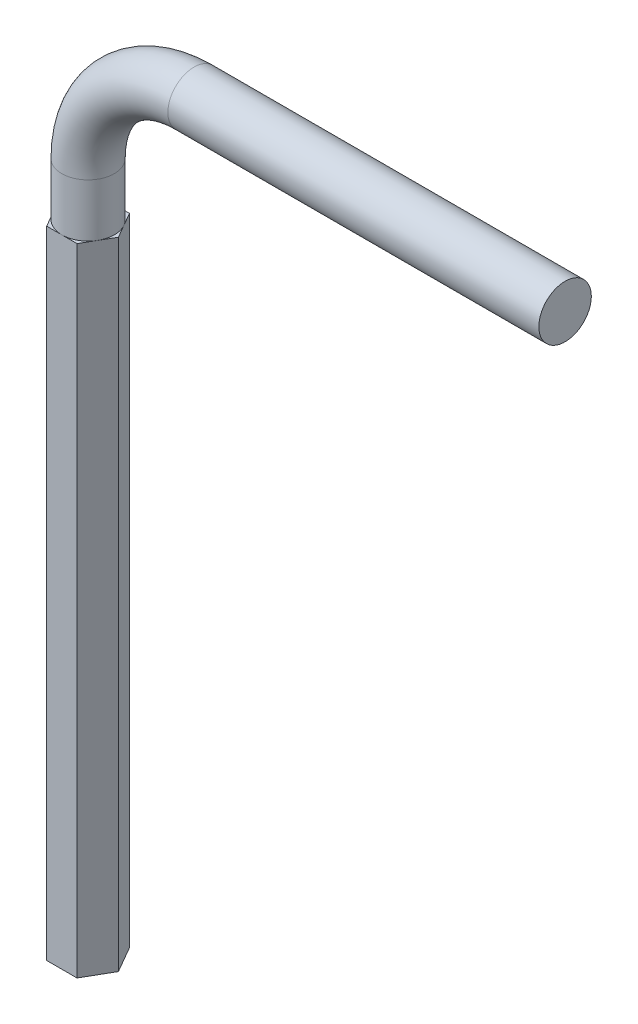
SolidWorks part; units mm, degrees
ref_plane "Front Plane" through (0, 0, 0) normal (0, 0, 1) x (1, 0, 0)
ref_plane "Top Plane" through (0, 0, 0) normal (0, 1, 0) x (1, 0, 0)
ref_plane "Right Plane" through (0, 0, 0) normal (1, 0, 0) x (0, 0, -1)
sketch "Sketch15" plane through (0, 0, 0) normal (0, 0, 1) x (1, 0, 0)
  line L0 (0, 0) -> (0, 65)
  line L1 (10, 75) -> (45, 75)
  arc A0 (0, 65) -> (10, 75) centre (10, 65) cw
  dimension "D1" = 10
sketch "Sketch16" plane through (0, 0, 0) normal (0, 1, 0) x (1, 0, 0)
  circle A0 centre (0, 0) radius 2.475
sweep "Sweep4" add profiles "Sketch16" path "Sketch15"
sketch "Sketch18" plane through (0, 0, 0) normal (0, 1, 0) x (1, 0, 0)
  line L1 (2.8579, 0) -> (1.4289, 2.475)
  line L2 (1.4289, 2.475) -> (-1.4289, 2.475)
  line L3 (-1.4289, 2.475) -> (-2.8579, 0)
  line L4 (-2.8579, 0) -> (-1.4289, -2.475)
  line L5 (-1.4289, -2.475) -> (1.4289, -2.475)
  line L6 (1.4289, -2.475) -> (2.8579, 0)
  circle A0 centre (0, 0) radius 2.475 construction
extrude "Boss-Extrude2" add sketch "Sketch18" along normal blind 60
